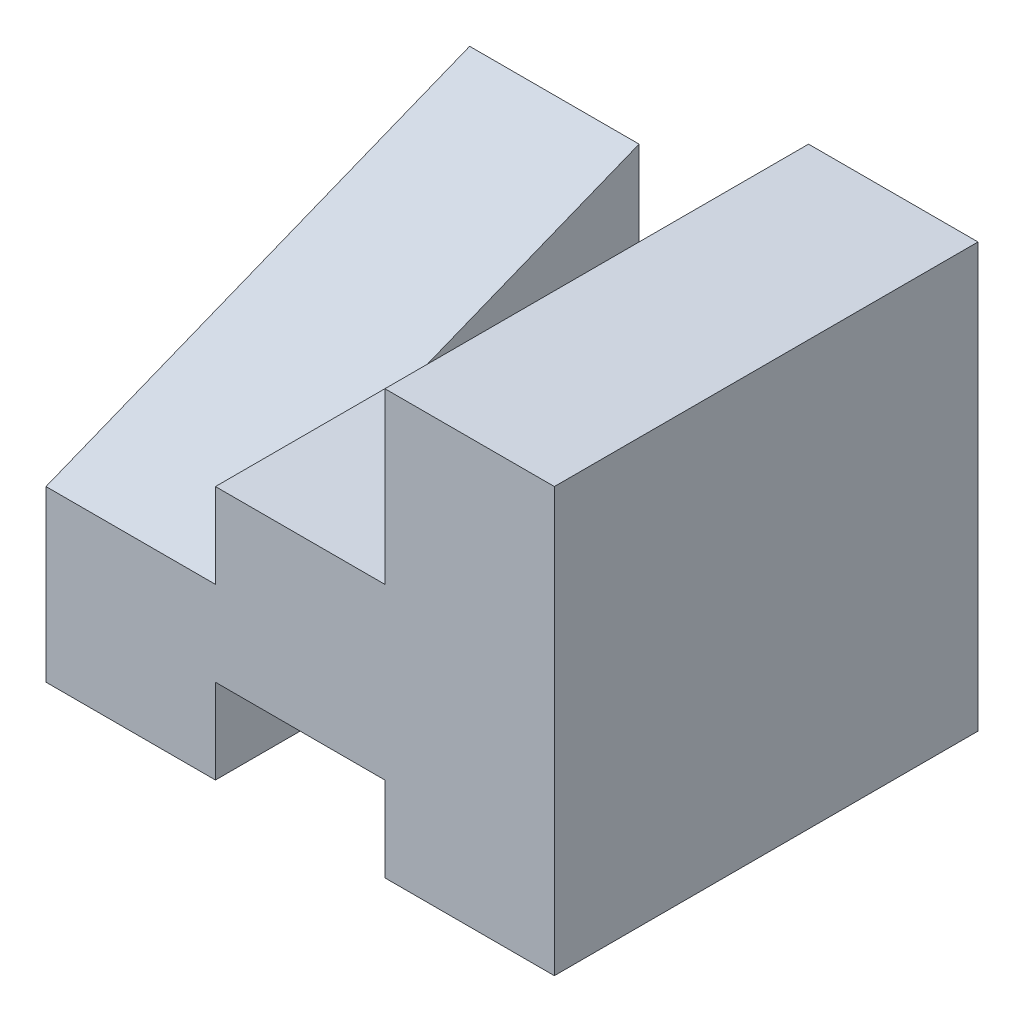
SolidWorks part; units mm, degrees
ref_plane "Front Plane" through (0, 0, 0) normal (0, 0, 1) x (1, 0, 0)
ref_plane "Top Plane" through (0, 0, 0) normal (0, 1, 0) x (1, 0, 0)
ref_plane "Right Plane" through (0, 0, 0) normal (1, 0, 0) x (0, 0, -1)
sketch "Sketch1" plane through (0, 0, 0) normal (0, 0, 1) x (1, 0, 0)
  line L0 (-30, 10) -> (-20, 10)
  line L1 (-20, 10) -> (-20, 15)
  line L2 (-20, 15) -> (-10, 15)
  line L3 (-10, 15) -> (-10, 25)
  line L4 (-10, 25) -> (0, 25)
  line L5 (0, 25) -> (0, 0)
  line L6 (0, 0) -> (-10, 0)
  line L7 (-10, 0) -> (-10, 5)
  line L8 (-10, 5) -> (-20, 5)
  line L9 (-20, 5) -> (-20, 0)
  line L10 (-20, 0) -> (-30, 0)
  line L11 (-30, 0) -> (-30, 10)
  dimension "D1" = 10
  dimension "D2" = 10
  dimension "D3" = 10
  dimension "D4" = 5
  dimension "D5" = 10
  dimension "D6" = 10
  dimension "D7" = 10
  dimension "D8" = 10
  dimension "D9" = 5
  dimension "D10" = 5
extrude "Boss-Extrude1" add sketch "Sketch1" along normal blind 25
sketch "Sketch2" plane through (-20, 0, 0) normal (-1, 0, 0) x (0, 0, 1)
  line L0 (0, 10) -> (0, 20)
  line L1 (0, 25) -> (0, 15) construction
  line L2 (0, 20) -> (25, 10)
  line L3 (25, 10) -> (0, 10)
  dimension "D1" = 10
extrude "Boss-Extrude2" add sketch "Sketch2" along normal blind 10
